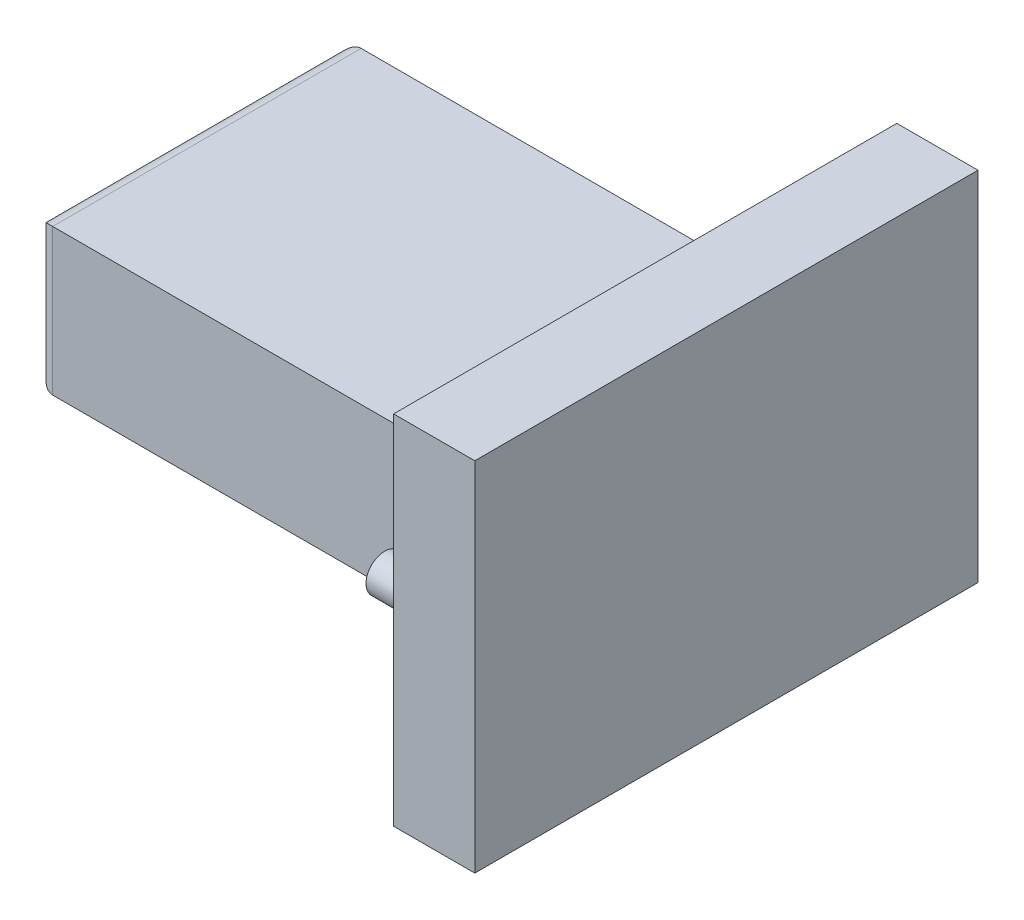
SolidWorks part; units mm, degrees
ref_plane "Front Plane" through (0, 0, 0) normal (0, 0, 1) x (1, 0, 0)
ref_plane "Top Plane" through (0, 0, 0) normal (0, 1, 0) x (1, 0, 0)
ref_plane "Right Plane" through (0, 0, 0) normal (1, 0, 0) x (0, 0, -1)
sketch "Sketch1" plane through (0, 0, 0) normal (1, 0, 0) x (0, 0, -1)
  line L1 (0, 0) -> (31, 0)
  line L2 (0, 0) -> (0, 22)
  line L3 (0, 22) -> (31, 22)
  line L4 (31, 0) -> (31, 22)
extrude "Boss-Extrude1" add sketch "Sketch1" along normal blind 5
sketch "Sketch2" plane through (0, 0, 0) normal (-1, 0, 0) x (0, 0, 1)
  line L1 (-25, 15.5) -> (-6, 15.5)
  line L2 (-25, 15.5) -> (-25, 6.5)
  line L3 (-25, 6.5) -> (-6, 6.5)
  line L4 (-6, 15.5) -> (-6, 6.5)
extrude "Boss-Extrude2" add sketch "Sketch2" along normal blind 28
fillet "Fillet1" radius 1 4 edges at (-28, 15.5, -15.5) (-28, 11, -6) (-28, 6.5, -15.5) (-28, 11, -25)
sketch "Sketch3" plane through (0, 0, 0) normal (-1, 0, 0) x (0, 0, 1)
  circle A0 centre (-2.25, 11) radius 1.15
extrude "Boss-Extrude3" add sketch "Sketch3" along normal blind 2.8
fillet "Fillet2" radius 0.1 1 edges at (0, 11, -1.1)
sketch "Sketch4" plane through (0, 0, 0) normal (-1, 0, 0) x (0, 0, 1)
  circle A0 centre (-28.75, 11) radius 1.15
extrude "Boss-Extrude4" add sketch "Sketch4" along normal blind 2.8
fillet "Fillet3" radius 0.1 1 edges at (0, 11, -27.6)
